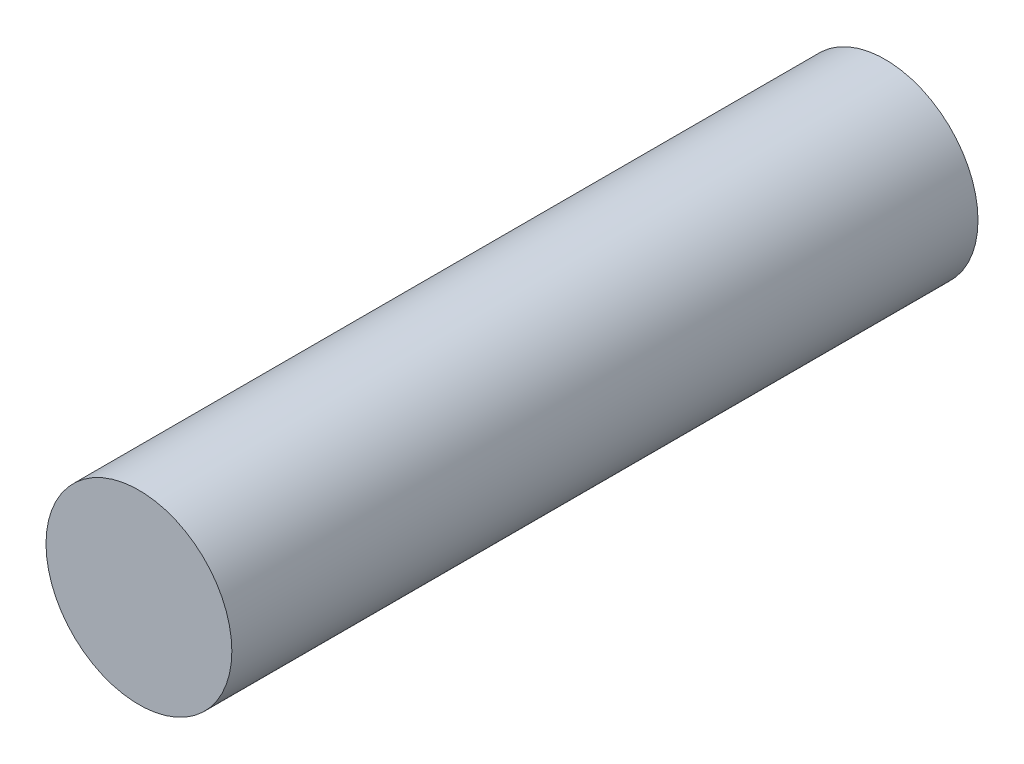
SolidWorks part; units mm, degrees
ref_plane "Front Plane" through (0, 0, 0) normal (0, 0, 1) x (1, 0, 0)
ref_plane "Top Plane" through (0, 0, 0) normal (0, 1, 0) x (1, 0, 0)
ref_plane "Right Plane" through (0, 0, 0) normal (1, 0, 0) x (0, 0, -1)
sketch "Sketch1" plane through (0, 0, 0) normal (0, 0, 1) x (1, 0, 0)
  circle A0 centre (0, 0) radius 24.875
  dimension "D1" = 49.75
extrude "Boss-Extrude1" add sketch "Sketch1" along normal blind 199.75
